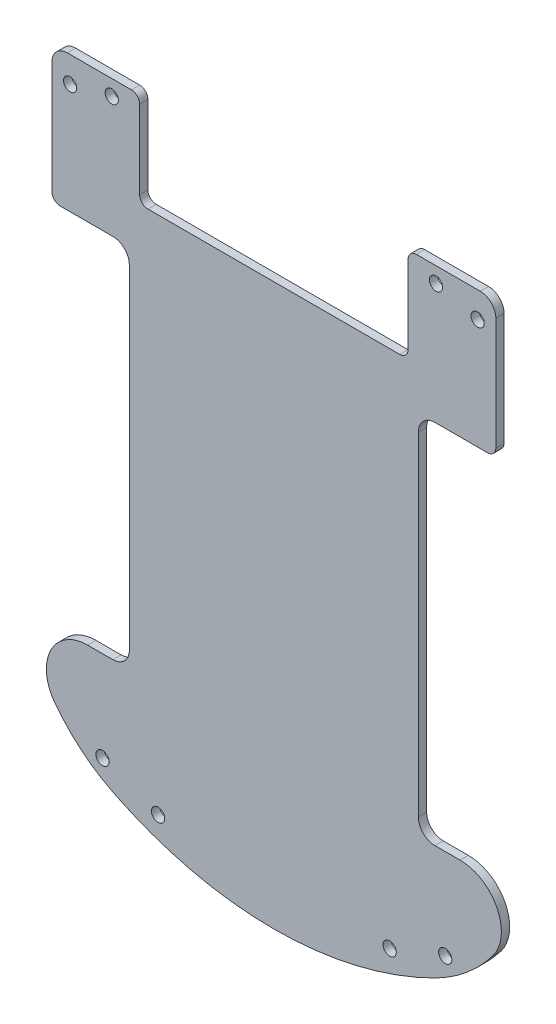
SolidWorks part; units mm, degrees
ref_plane "Front Plane" through (0, 0, 0) normal (0, 0, 1) x (1, 0, 0)
ref_plane "Top Plane" through (0, 0, 0) normal (0, 1, 0) x (1, 0, 0)
ref_plane "Right Plane" through (0, 0, 0) normal (1, 0, 0) x (0, 0, -1)
ref_plane "Plane1" through (0, 0, 0) normal (0, 0, -1) x (-1, 0, 0)
sketch "Sketch1" plane through (0, 0, 0) normal (0, 0, -1) x (-1, 0, 0)
  line L0 (50, 71.75) -> (34.5, 71.75)
  line L1 (32.5, 69.75) -> (32.5, 50.75)
  line L2 (30.5, 48.75) -> (-30.5, 48.75)
  line L3 (-32.5, 50.75) -> (-32.5, 69.75)
  line L4 (-34.5, 71.75) -> (-50, 71.75)
  line L5 (-53.75, 68) -> (-53.75, 40.75)
  line L6 (-51.75, 38.75) -> (-39, 38.75)
  line L7 (-35, 34.75) -> (-35, -46)
  line L8 (-39, -50) -> (-45.095, -50)
  line L9 (45.095, -50) -> (39, -50)
  line L10 (35, -46) -> (35, 34.75)
  line L11 (39, 38.75) -> (51.75, 38.75)
  line L12 (53.75, 40.75) -> (53.75, 68)
  line L13 (0, 0) -> (0, -87) construction
  line L14 (0, 0) -> (49.3488, 65.4881) construction
  line L15 (0, 0) -> (-49.3488, 65.4881) construction
  line L16 (0, 0) -> (28.0457, -77.0548) construction
  line L17 (0, 0) -> (-28.0457, -77.0548) construction
  circle A9 centre (49.3488, 65.4881) radius 1.6
  circle A10 centre (-49.3488, 65.4881) radius 1.6
  circle A32 centre (28.0457, -77.0548) radius 1.6
  circle A33 centre (-28.0457, -77.0548) radius 1.6
  arc A34 (34.5, 71.75) -> (32.5, 69.75) centre (34.5, 69.75) ccw
  arc A35 (32.5, 50.75) -> (30.5, 48.75) centre (30.5, 50.75) cw
  arc A36 (-30.5, 48.75) -> (-32.5, 50.75) centre (-30.5, 50.75) cw
  arc A37 (-32.5, 69.75) -> (-34.5, 71.75) centre (-34.5, 69.75) ccw
  arc A38 (-50, 71.75) -> (-53.75, 68) centre (-50, 68) ccw
  arc A39 (-53.75, 40.75) -> (-51.75, 38.75) centre (-51.75, 40.75) ccw
  arc A40 (-39, 38.75) -> (-35, 34.75) centre (-39, 34.75) cw
  arc A41 (-35, -46) -> (-39, -50) centre (-39, -46) cw
  arc A42 (-45.095, -50) -> (-53.095, -66) centre (-45.095, -60) ccw
  arc A43 (-53.095, -66) -> (-39.0482, -77.7447) centre (-21.095, -42) ccw
  arc A44 (-39.0482, -77.7447) -> (39.0482, -77.7447) centre (0, 0) ccw
  arc A45 (39.0482, -77.7447) -> (53.095, -66) centre (21.095, -42) ccw
  arc A46 (53.095, -66) -> (45.095, -50) centre (45.095, -60) ccw
  arc A47 (39, -50) -> (35, -46) centre (39, -46) cw
  arc A48 (35, 34.75) -> (39, 38.75) centre (39, 34.75) cw
  arc A49 (51.75, 38.75) -> (53.75, 40.75) centre (51.75, 40.75) ccw
  arc A50 (53.75, 68) -> (50, 71.75) centre (50, 68) ccw
extrude "Boss-Extrude1" add sketch "Sketch1" against normal blind 2
sketch "Sketch2" plane through (0, 0, 2) normal (0, 0, 1) x (1, 0, 0)
  line L0 (0, 0) -> (-41.5, -71.8801) construction
  line L1 (0, 0) -> (41.5, -71.8801) construction
  line L2 (0, 0) -> (39.2598, 68) construction
  line L3 (0, 0) -> (-39.2598, 68) construction
  line L4 (-47.2117, 68) -> (64.0051, 68) construction
  dimension "D1" = 68
hole_wizard "M3 Clearance Hole1" positions "3DSketch1" profile "Sketch3" hole size "M3" standard "ANSI Metric"
sketch3d "3DSketch1"
  point P0 (-39.2598, 68, 2)
  point P3 (39.2598, 68, 2)
  point P6 (41.5, -71.8801, 2)
  point P9 (-41.5, -71.8801, 2)
sketch "Sketch3" plane through (-39.2598, 68, 2) normal (1, 0, 0) x (0, -1, 0)
  line L0 (0, 0) -> (0, 2.9614)
  line L1 (0, 2.9614) -> (1.6, 2)
  line L2 (1.6, 2) -> (1.6, 0)
  line L5 (1.6, 0) -> (0, 0)
  line L10 (0, 2.9614) -> (-1.6, 2) construction
  line L11 (0, -6.35) -> (0, 107.95) construction
  dimension "Hole Dia." = 3.2
  dimension "Hole Depth" = 2
  dimension "Drill Angle" = 118
